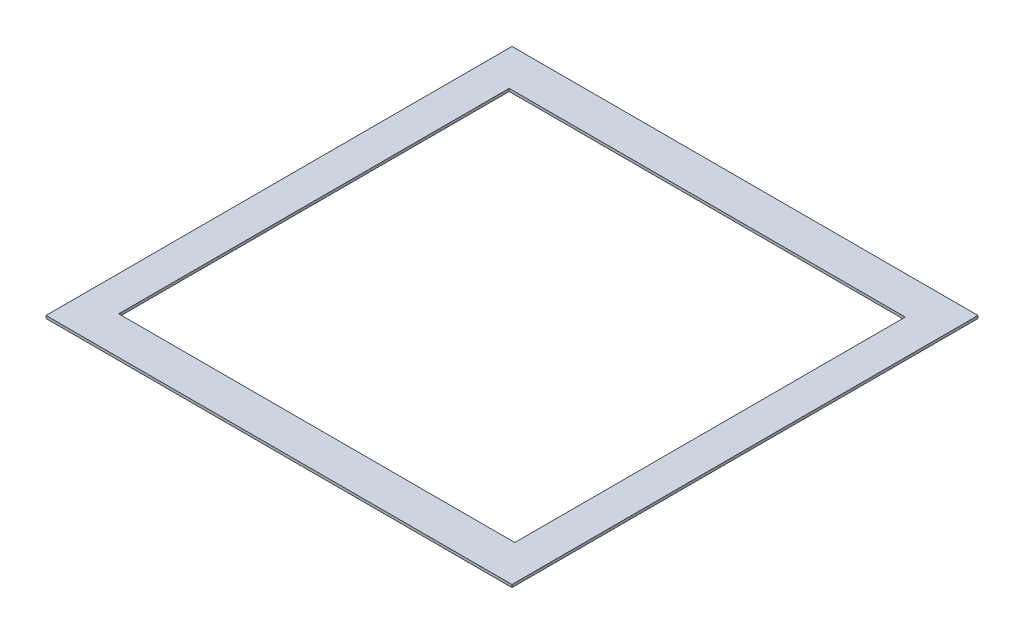
SolidWorks part; units mm, degrees
ref_plane "前视基准面" through (0, 0, 0) normal (0, 0, 1) x (1, 0, 0)
ref_plane "上视基准面" through (0, 0, 0) normal (0, 1, 0) x (1, 0, 0)
ref_plane "右视基准面" through (0, 0, 0) normal (1, 0, 0) x (0, 0, -1)
sketch "草图2" plane through (0, 0, 0) normal (0, 1, 0) x (1, 0, 0)
  line B0 (-1126.4698, 2110.5701) -> (-1126.4698, -68.087)
  line B1 (1083.4958, -68.087) -> (1083.4958, 2110.5701)
  line B2 (1083.4958, 2110.5701) -> (-1126.4698, 2110.5701)
sketch_block_instance "块-Tingsquare-1"
sketch_block "块1"
sketch "草图3" plane through (0, 0, 0) normal (0, 1, 0) x (1, 0, 0)
  line L1 (-1126.4698, 2110.5701) -> (1083.4958, 2110.5701)
  line L2 (-1321.487, 2321.2415) -> (1278.513, 2321.2415)
  line L3 (-1321.487, 2321.2415) -> (-1321.487, -278.7585)
  line L4 (-1321.487, -278.7585) -> (1278.513, -278.7585)
  line L5 (1278.513, 2321.2415) -> (1278.513, -278.7585)
  line L8 (1083.4958, 2110.5701) -> (1083.4958, -68.087)
  line L9 (1083.4958, -68.087) -> (-1126.4698, -68.087)
  line L10 (-1126.4698, -68.087) -> (-1126.4698, 2110.5701)
  point P4 (-21.487, 1021.2415)
extrude "凸台-拉伸2" add sketch "草图3" along normal blind 15
